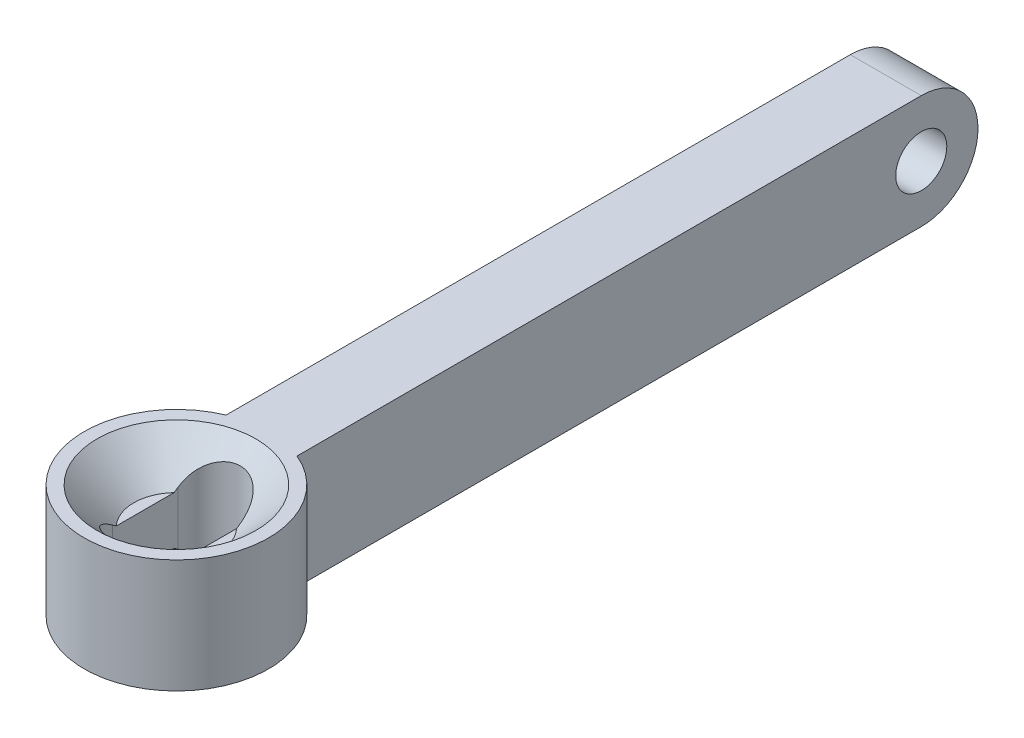
SolidWorks part; units mm, degrees
ref_plane "前视基准面" through (0, 0, 0) normal (0, 0, 1) x (1, 0, 0)
ref_plane "上视基准面" through (0, 0, 0) normal (0, 1, 0) x (1, 0, 0)
ref_plane "右视基准面" through (0, 0, 0) normal (1, 0, 0) x (0, 0, -1)
sketch "Sketch1" plane through (0, 0, 0) normal (0, 1, 0) x (1, 0, 0)
  line L0 (0, 1.15) -> (0, -1.15) construction
  line L1 (1.1, 1.15) -> (1.1, -1.15)
  line L2 (-1.1, 1.15) -> (-1.1, -1.15)
  arc A0 (1.1, 1.15) -> (-1.1, 1.15) centre (0, 1.15) ccw
  arc A1 (-1.1, -1.15) -> (1.1, -1.15) centre (0, -1.15) ccw
  circle A2 centre (0, 0) radius 3.25
  point P3 (0, 0)
  dimension "D1" = 2.3
  dimension "D3" = 6.5
  dimension "D2" = 2.2
extrude "Extrude1" add sketch "Sketch1" along normal blind 4
sketch "Sketch2" plane through (0, 0, 0) normal (1, 0, 0) x (0, 0, -1)
  line L0 (3, 4) -> (3, 0)
  line L1 (3, 0) -> (25, 0)
  line L2 (3, 4) -> (25, 4)
  line L3 (3, 2) -> (20.1785, 2) construction
  line L4 (-3.25, 0) -> (3.25, 0) construction
  line L5 (0, -0.1854) -> (0, 8.9684) construction
  line L7 (3.25, 4) -> (-3.25, 4) construction
  arc A0 (25, 0) -> (25, 4) centre (25, 2) ccw
  circle A1 centre (25, 2) radius 0.9
  dimension "D1" = 1.8
  dimension "D2" = 22
  dimension "D3" = 3
extrude "Extrude2" add sketch "Sketch2" along normal mid plane 2.5
sketch "Sketch4" plane through (0, 0, 0) normal (1, 0, 0) x (0, 0, -1)
  line L0 (0, 0) -> (0, 11.1604) construction
  line L1 (0, 2.7) -> (1.5, 2.7)
  line L2 (1.5, 2.7) -> (2.8, 4)
  line L3 (3, 4) -> (-3.25, 4) construction
  line L4 (2.8, 4) -> (0, 4)
  line L5 (0, 4) -> (0, 2.7)
  line L6 (0, 1) -> (1.5, 1)
  line L7 (1.5, 1) -> (2.5, 0)
  line L8 (-3.25, 0) -> (3, 0) construction
  line L9 (2.5, 0) -> (0, 0)
  line L10 (0, 0) -> (0, 1)
  dimension "D1" = 135
  dimension "D2" = 2.8
  dimension "D3" = 1.5
  dimension "D4" = 135
  dimension "D5" = 2.5
  dimension "D6" = 1.5
revolve "Cut-Revolve1" cut sketch "Sketch4" angle 360 about L0
